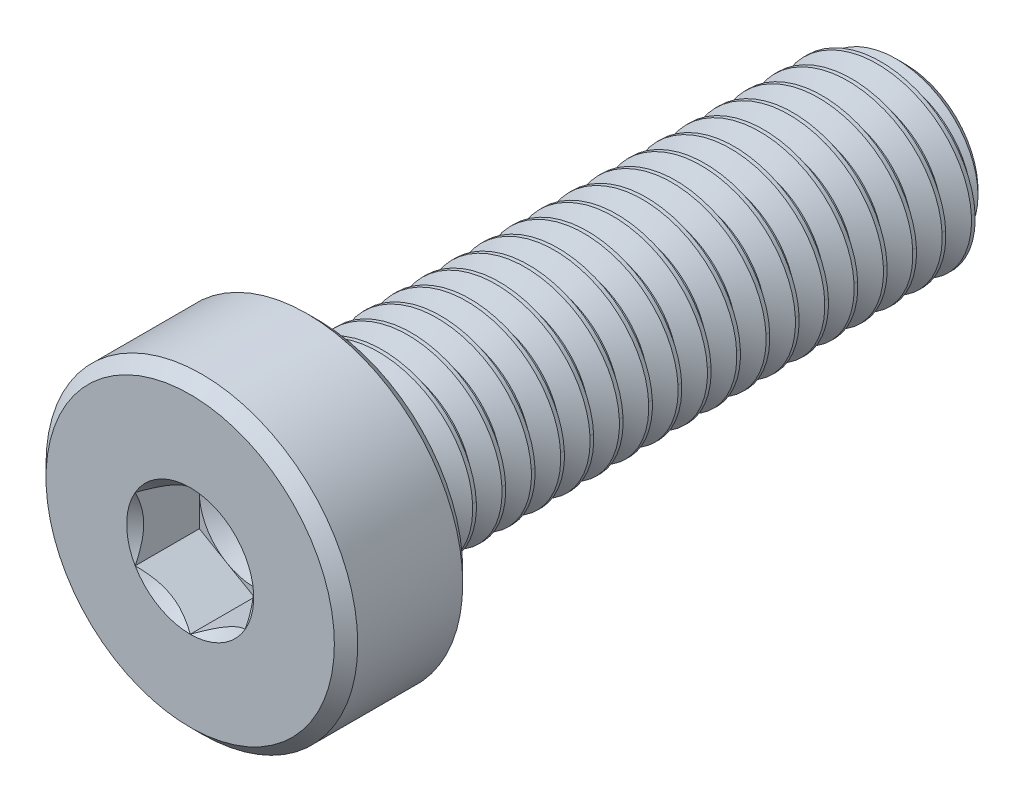
SolidWorks part; units mm, degrees
ref_plane "Front Plane" through (0, 0, 0) normal (0, 0, 1) x (1, 0, 0)
ref_plane "Top Plane" through (0, 0, 0) normal (0, 1, 0) x (1, 0, 0)
ref_plane "Right Plane" through (0, 0, 0) normal (1, 0, 0) x (0, 0, -1)
sketch "Sketch1" plane through (0, 0, 0) normal (1, 0, 0) x (0, 0, -1)
  line L0 (9.75, 0) -> (-9.75, 0) construction
  line L1 (-9.75, -4.25) -> (-9.75, 4.25) construction
  line L2 (-9.75, 4.25) -> (-6.25, 4.25) construction
  line L3 (9.75, -2.5) -> (9.75, 2.5) construction
  line L7 (9.7, 2.5866) -> (10.5, 2.5866) construction
  line L8 (10.5, 2.5866) -> (10.1, 1.8938) construction
  line L9 (10.1, 1.8938) -> (9.7, 2.5866) construction
  line L10 (10.1, 2.5866) -> (10.1, 2.5) construction
  line L11 (10.1, 2.5) -> (10.1, 1.9804) construction
  line L12 (10.1, 1.9804) -> (10.1, 1.8938) construction
  line L13 (10.05, 1.9804) -> (10.15, 1.9804) construction
  line L14 (9.75, 2.5) -> (10.45, 2.5) construction
  line L15 (9.725, 2.5433) -> (10.475, 2.5433) construction
  line L17 (9.75, -2.5) -> (7.75, -2.5) construction
  point P4 (0, 0)
  point P8 (-9.75, 0)
  point P11 (9.75, 0)
  point P16 (-9.75, 1.5)
  point P20 (10.1, 1.9804)
  point P23 (10.1, 2.5)
  point P26 (10.1, 2.5433)
  point P27 (-9.75, -1.5)
  dimension "Head Diameter" = 8.5
  dimension "Head Height" = 3.5
  dimension "Length" = 16
  dimension "Thread Size" = 5
  dimension "Thread Pitch" = 0.8
  dimension "D1" = 0.1
  dimension "Drive Size" = 3
  dimension "D2" = 2
sketch "Sketch2" plane through (0, 0, 0) normal (1, 0, 0) x (0, 0, -1)
  line L0 (-6.5687, 4.25) -> (-6.25, 3.9312)
  line L1 (-9.75, 4.25) -> (-6.25, 4.25) construction
  line L2 (-9.75, 1.5) -> (-8, 1.5)
  line L3 (-8, 1.5) -> (-8, 0)
  line L4 (9.75, 0) -> (-9.75, 0) construction
  line L5 (-8, 0) -> (9.75, 0)
  line L6 (9.75, 0) -> (9.75, 1.9804)
  line L7 (9.75, -2.5) -> (9.75, 2.5) construction
  line L8 (9.75, 1.9804) -> (9.2304, 2.5)
  line L9 (9.2304, 2.5) -> (-6, 2.5)
  line L10 (-6.25, 2.75) -> (-6.25, 3.9312)
  line L11 (-9.75, 1.5) -> (-9.75, 3.9312)
  line L12 (-9.75, -4.25) -> (-9.75, 4.25) construction
  line L13 (-9.75, 3.9312) -> (-9.4312, 4.25)
  line L14 (-9.4312, 4.25) -> (-6.5687, 4.25)
  arc A0 (-6, 2.5) -> (-6.25, 2.75) centre (-6, 2.75) cw
  point P24 (-6.25, 2.5)
  dimension "D6" = 0.25
  dimension "D1" = 45
  dimension "D3" = 1.75
  dimension "D4" = 45
  dimension "D5" = 0.3187
  dimension "D2" = 0.3187
revolve "Revolve1" add sketch "Sketch2" angle 360 about L5
sketch "Sketch3" plane through (0, 0, 9.75) normal (0, 0, 1) x (1, 0, 0)
  line L5 (0, 1.7321) -> (-1.5, 0.866)
  line L7 (-1.5, 0.866) -> (-1.5, -0.866)
  line L8 (-1.5, -0.866) -> (0, -1.7321)
  line L9 (0, -1.7321) -> (1.5, -0.866)
  line L10 (1.5, -0.866) -> (1.5, 0.866)
  line L11 (1.5, 0.866) -> (0, 1.7321)
  circle A1 centre (0, 0) radius 1.5 construction
  circle A2 centre (0, 0) radius 1.5 construction
extrude "Cut-Extrude1" cut sketch "Sketch3" against normal up to surface (1.75 mm away) up to face at (1.5, 0, 8)
sketch "Sketch4" plane through (0, 0, 9.75) normal (0, 0, 1) x (1, 0, 0)
  circle A0 centre (0, 0) radius 1.7321
extrude "Cut-Extrude2" cut sketch "Sketch4" against normal through all draft 45
sketch "Sketch6" plane through (0, 0, 8) normal (0, 0, 1) x (1, 0, 0)
  line L0 (-1.5, 0.866) -> (-1.5, -0.866) construction
  circle A1 centre (0, 0) radius 1.5
extrude "Cut-Extrude5" cut sketch "Sketch6" against normal through all draft 60
sketch "Sketch7" plane through (0, 0, -9.75) normal (0, 0, -1) x (-1, 0, 0)
  circle A0 centre (0, 0) radius 2.5
curve "Helix/Spiral1" pitch 0.8 height 16.5 turns 20.625
sketch "Sketch8" plane through (0, 0, 0) normal (1, 0, 0) x (0, 0, -1)
  line L0 (9.725, 2.5433) -> (10.475, 2.5433)
  line L1 (10.475, 2.5433) -> (10.15, 1.9804)
  line L2 (10.15, 1.9804) -> (10.05, 1.9804)
  line L3 (10.05, 1.9804) -> (9.725, 2.5433)
sweep "Cut-Sweep1" cut profiles "Sketch8" path "Helix/Spiral1"
sketch "Sketch9" plane through (0, 0, 0) normal (1, 0, 0) x (0, 0, -1)
  line L0 (-6.8, 0) -> (-6.8, 2.75)
  line L1 (9.75, 0) -> (-9.75, 0) construction
  line L2 (-6, 2.5) -> (-5.45, 2.5)
  line L3 (-5.45, 2.5) -> (-4.0066, 0)
  line L4 (-4.0066, 0) -> (-6.8, 0)
  line L5 (9.75, 2.5) -> (10.45, 2.5) construction
  line L7 (-6.25, -3.9312) -> (-6.25, 3.9312) construction
  line L8 (-8, 0) -> (9.75, 0) construction
  line L9 (9.75, 0) -> (9.75, 1.9804) construction
  line L10 (-6.8, 2.75) -> (-6.25, 2.75)
  arc A0 (-6.25, 2.75) -> (-6, 2.5) centre (-6, 2.75) ccw construction
  arc A1 (-6.25, 2.75) -> (-6, 2.5) centre (-6, 2.75) ccw
  dimension "D1" = 60
  dimension "D2" = 0.8
  dimension "D3" = 16.55
revolve "Revolve2" add sketch "Sketch9" angle 360 about L4
equation "\"D1@Sketch1\"=\"Thread Pitch@Sketch1\"/8"
equation "\"D5@Sketch2\"=\"D2@Sketch2\""
equation "\"D3@Helix/Spiral1\"=\"Length@Sketch1\"+\"Thread Pitch@Sketch1\"*0.625"
equation "\"D4@Helix/Spiral1\"=\"Thread Pitch@Sketch1\""
equation "\"D2@Sketch2\"=\"Head Diameter@Sketch1\"*0.0375"
equation "\"D2@Sketch1\"=\"Thread Pitch@Sketch1\"*2.5"
equation "\"D3@Sketch2\"=\"Head Height@Sketch1\"*0.5"
equation "\"60g\"=45"
equation "\"D6@Sketch2\" = \"Thread Size@Sketch1\" * 0.05"
equation "\"D2@Sketch9\"=\"Thread Pitch@Sketch1\""
equation "\"D3@Sketch9\"=\"D3@Helix/Spiral1\"+\"D1@Sketch1\"*0.5"
